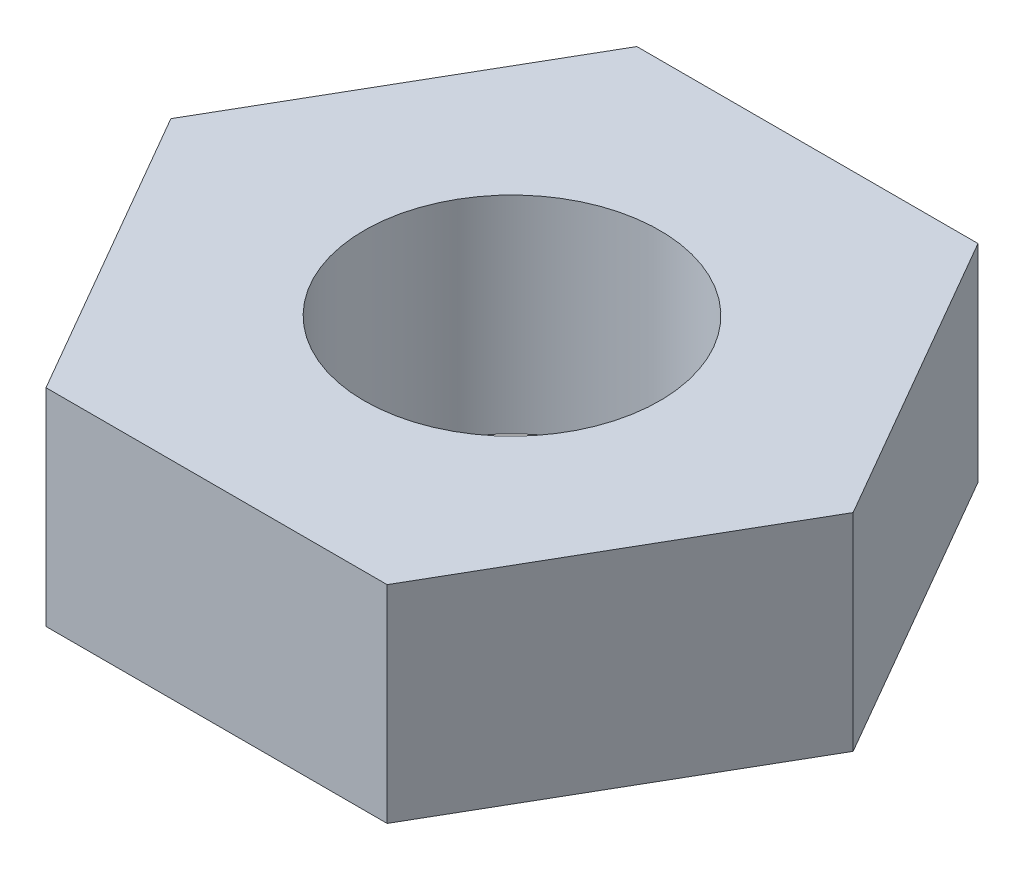
SolidWorks part; units mm, degrees
ref_plane "Front Plane" through (0, 0, 0) normal (0, 0, 1) x (1, 0, 0)
ref_plane "Top Plane" through (0, 0, 0) normal (0, 1, 0) x (1, 0, 0)
ref_plane "Right Plane" through (0, 0, 0) normal (1, 0, 0) x (0, 0, -1)
sketch "Sketch1" plane through (0, 0, 0) normal (0, 1, 0) x (1, 0, 0)
  line L1 (5.7735, 0) -> (2.8868, 5)
  line L2 (2.8868, 5) -> (-2.8868, 5)
  line L3 (-2.8868, 5) -> (-5.7735, 0)
  line L4 (-5.7735, 0) -> (-2.8868, -5)
  line L5 (-2.8868, -5) -> (2.8868, -5)
  line L6 (2.8868, -5) -> (5.7735, 0)
  circle A0 centre (0, 0) radius 5 construction
  circle A1 centre (0, 0) radius 2.5
  dimension "D1" = 10
  dimension "D2" = 5
extrude "Boss-Extrude1" add sketch "Sketch1" along normal blind 3.5
